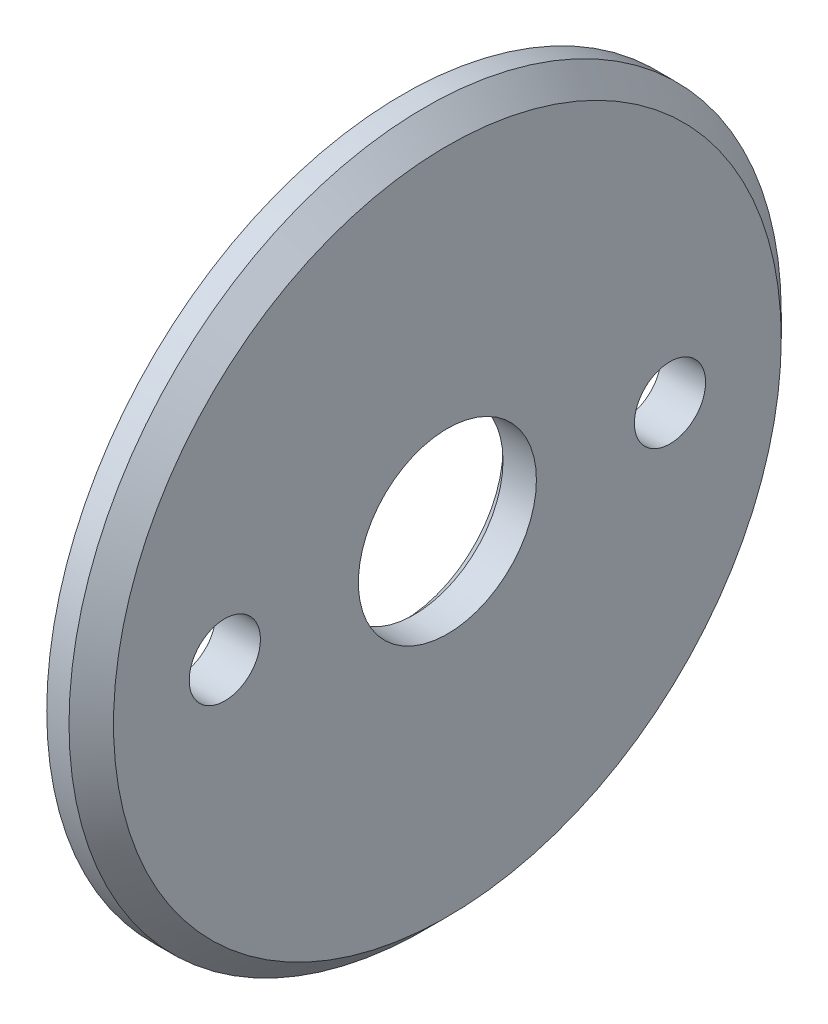
SolidWorks part; units mm, degrees
ref_plane "Front Plane" through (0, 0, 0) normal (0, 0, 1) x (1, 0, 0)
ref_plane "Top Plane" through (0, 0, 0) normal (0, 1, 0) x (1, 0, 0)
ref_plane "Right Plane" through (0, 0, 0) normal (1, 0, 0) x (0, 0, -1)
sketch "Sketch1" plane through (0, 0, 0) normal (1, 0, 0) x (0, 0, -1)
  circle A0 centre (0, 0) radius 16
  circle A1 centre (0, 0) radius 4
  dimension "D1" = 32
  dimension "D2" = 8
extrude "Boss-Extrude1" add sketch "Sketch1" along normal blind 2
sketch "Sketch2" plane through (2, 0, 0) normal (1, 0, 0) x (0, 0, -1)
  line L0 (0, 0) -> (50000, 0) construction
  line L1 (0, 0) -> (0, 50000) construction
  circle A0 centre (-10, 0) radius 1.6
  circle A1 centre (10, 0) radius 1.6
  dimension "D2" = 3.2
  dimension "D1" = 20
extrude "Cut-Extrude1" cut sketch "Sketch2" against normal through all
chamfer "Chamfer1" distance 1 angle 45 1 edges at (2, 0, -16)
chamfer "Chamfer2" distance 0.5 angle 45 1 edges at (0, 0, -4)
